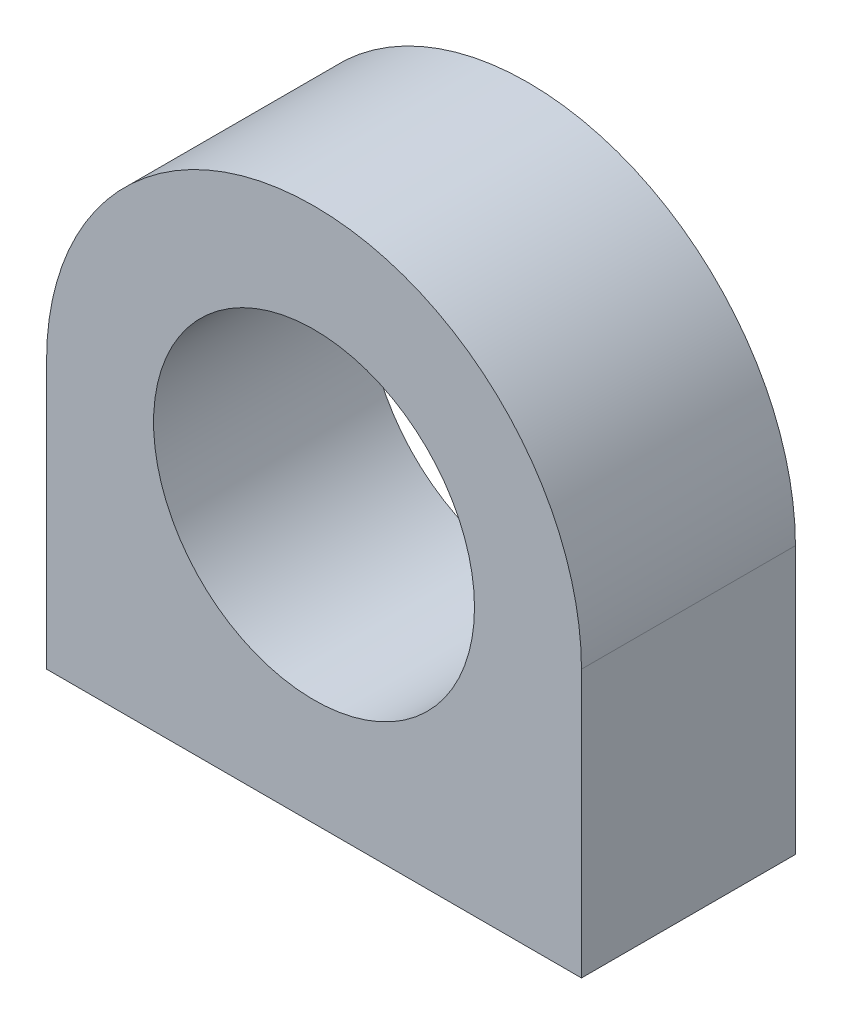
SolidWorks part; units mm, degrees
ref_plane "Front" through (0, 0, 0) normal (0, 0, 1) x (1, 0, 0)
ref_plane "Top" through (0, 0, 0) normal (0, 1, 0) x (1, 0, 0)
ref_plane "Right" through (0, 0, 0) normal (1, 0, 0) x (0, 0, -1)
sketch "Sketch1" plane through (0, 0, 0) normal (0, 0, 1) x (1, 0, 0)
  line L1 (-5, -2.5) -> (5, -2.5)
  line L2 (-5, -2.5) -> (-5, 2.5)
  line L4 (5, -2.5) -> (5, 2.5)
  arc A0 (-5, 2.5) -> (5, 2.5) centre (0, 2.5) cw
  circle A1 centre (0, 2.5) radius 3
  point P0 (0, 0)
  dimension "D3" = 6
  dimension "D1" = 10
  dimension "D2" = 5
extrude "Boss-Extrude1" add sketch "Sketch1" along normal blind 4
